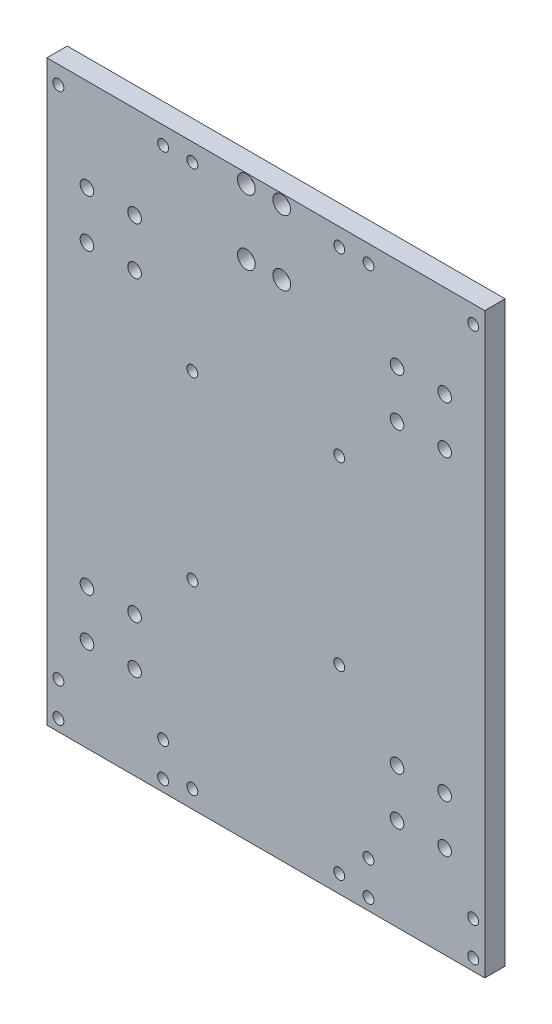
SolidWorks part; units mm, degrees
ref_plane "Płaszczyzna przednia" through (0, 0, 0) normal (0, 0, 1) x (1, 0, 0)
ref_plane "Płaszczyzna górna" through (0, 0, 0) normal (0, 1, 0) x (1, 0, 0)
ref_plane "Płaszczyzna prawa" through (0, 0, 0) normal (1, 0, 0) x (0, 0, -1)
sketch "Szkic1" plane through (0, 0, 0) normal (0, 0, 1) x (1, 0, 0)
  line L1 (161, -212.5) -> (-161, -212.5)
  line L2 (161, -212.5) -> (161, 212.5)
  line L3 (161, 212.5) -> (-161, 212.5)
  line L4 (-161, -212.5) -> (-161, 212.5)
  line L5 (161, -212.5) -> (-161, 212.5) construction
  line L6 (161, 212.5) -> (-161, -212.5) construction
  point P0 (0, 0)
  dimension "D1" = 322
  dimension "D2" = 425
extrude "Dodanie-wyciągnięcie1" add sketch "Szkic1" along normal blind 15
sketch "Szkic2" plane through (0, 0, 15) normal (0, 0, 1) x (1, 0, 0)
  line L0 (161, 212.5) -> (-161, 212.5) construction
  line L1 (-161, 212.5) -> (-161, -212.5) construction
  circle A0 centre (-131.5, 144.5) radius 3
  dimension "D1" = 68
  dimension "D3" = 6
  dimension "D2" = 29.5
extrude "Wytnij-wyciągnięcie1" cut sketch "Szkic2" against normal blind 15
sketch "Szkic3" plane through (0, 0, 15) normal (0, 0, 1) x (1, 0, 0)
  circle A0 centre (-131.5, 144.5) radius 5
  dimension "D1" = 10
extrude "Wytnij-wyciągnięcie2" cut sketch "Szkic3" against normal blind 7
pattern_linear "Szyk liniowy1" count 2 spacing 35 along (1, 0, 0) count 2 spacing 35 along (0, -1, 0) of "Wytnij-wyciągnięcie1", "Wytnij-wyciągnięcie2"
pattern_linear "Szyk liniowy2" count 2 spacing 228 along (1, 0, 0) count 2 spacing 254 along (0, -1, 0) of "Szyk liniowy1", "Wytnij-wyciągnięcie1", "Wytnij-wyciągnięcie2"
sketch "Szkic6" plane through (0, 0, 15) normal (0, 0, 1) x (1, 0, 0)
  line L0 (-161, 212.5) -> (-161, -212.5) construction
  line L1 (161, 212.5) -> (-161, 212.5) construction
  circle A0 centre (-152.5, 199.5) radius 4
  circle A1 centre (-75.5, 199.5) radius 4
  dimension "D1" = 8
  dimension "D2" = 8
  dimension "D3" = 8.5
  dimension "D4" = 13
  dimension "D5" = 77
extrude "Wytnij-wyciągnięcie3" cut sketch "Szkic6" against normal blind 20
sketch "Szkic7" plane through (0, 0, 15) normal (0, 0, 1) x (1, 0, 0)
  line L0 (-161, 212.5) -> (-161, -212.5) construction
  line L1 (-161, -212.5) -> (161, -212.5) construction
  circle A0 centre (-152.5, -204) radius 4
  circle A1 centre (-152.5, -179) radius 4
  circle A2 centre (-75.5, -204) radius 4
  circle A3 centre (-75.5, -179) radius 4
  dimension "D1" = 8
  dimension "D2" = 8
  dimension "D3" = 8
  dimension "D4" = 8
  dimension "D5" = 8.5
  dimension "D6" = 8.5
  dimension "D7" = 25
  dimension "D8" = 77
extrude "Wytnij-wyciągnięcie4" cut sketch "Szkic7" against normal blind 20
sketch "Szkic10" plane through (0, 0, 15) normal (0, 0, 1) x (1, 0, 0)
  line L0 (161, 212.5) -> (-161, 212.5) construction
  line L1 (161, -212.5) -> (161, 212.5) construction
  circle A0 centre (75.5, 199.5) radius 4
  circle A1 centre (152.5, 199.5) radius 4
  dimension "D1" = 8
  dimension "D2" = 8
  dimension "D3" = 77
  dimension "D4" = 13
  dimension "D5" = 8.5
extrude "Wytnij-wyciągnięcie5" cut sketch "Szkic10" against normal blind 21
sketch "Szkic11" plane through (0, 0, 15) normal (0, 0, 1) x (1, 0, 0)
  line L0 (161, -212.5) -> (161, 212.5) construction
  line L2 (-161, -212.5) -> (161, -212.5) construction
  circle A0 centre (152.5, -179) radius 4
  circle A1 centre (152.5, -204) radius 4
  circle A2 centre (75.5, -204) radius 4
  circle A3 centre (75.5, -179) radius 4
  dimension "D1" = 8.5
  dimension "D5" = 8
  dimension "D6" = 8
  dimension "D7" = 8
  dimension "D8" = 8
  dimension "D2" = 8.5
  dimension "D3" = 25
  dimension "D4" = 77
extrude "Wytnij-wyciągnięcie6" cut sketch "Szkic11" against normal blind 21
sketch "Szkic12" plane through (0, 0, 15) normal (0, 0, 1) x (1, 0, 0)
  line L0 (161, 212.5) -> (-161, 212.5) construction
  circle A0 centre (-14.3, 205.5) radius 4
  circle A1 centre (-75.5, 199.5) radius 4 construction
  circle A2 centre (11.7, 205.5) radius 4
  circle A3 centre (-14.3, 157.5) radius 4
  circle A4 centre (11.7, 157.5) radius 4
  dimension "D1" = 7
  dimension "D3" = 26
  dimension "D4" = 48
  dimension "D5" = 8
  dimension "D6" = 8
  dimension "D7" = 8
  dimension "D8" = 8
  dimension "D2" = 61.2
extrude "Wytnij-wyciągnięcie7" cut sketch "Szkic12" against normal blind 15
sketch "Szkic13" plane through (0, 0, 15) normal (0, 0, 1) x (1, 0, 0)
  circle A0 centre (-14.3, 205.5) radius 6.5
  circle A1 centre (11.7, 205.5) radius 6.5
  circle A2 centre (11.7, 157.5) radius 6.5
  circle A3 centre (-14.3, 157.5) radius 6.5
  dimension "D1" = 13
  dimension "D2" = 13
  dimension "D3" = 13
  dimension "D4" = 13
extrude "Wytnij-wyciągnięcie8" cut sketch "Szkic13" against normal blind 9
sketch "Szkic14" plane through (0, 0, 15) normal (0, 0, 1) x (1, 0, 0)
  line L0 (161, 212.5) -> (-161, 212.5) construction
  line L1 (-161, 212.5) -> (-161, -212.5) construction
  circle A0 centre (-54, 199.5) radius 4
  circle A1 centre (54, 199.5) radius 4
  dimension "D1" = 13
  dimension "D4" = 8
  dimension "D5" = 8
  dimension "D2" = 107
  dimension "D3" = 108
extrude "Wytnij-wyciągnięcie9" cut sketch "Szkic14" against normal blind 15
pattern_linear "Szyk liniowy3" count 4 spacing 133 along (0, -1, 0) of "Wytnij-wyciągnięcie9"
